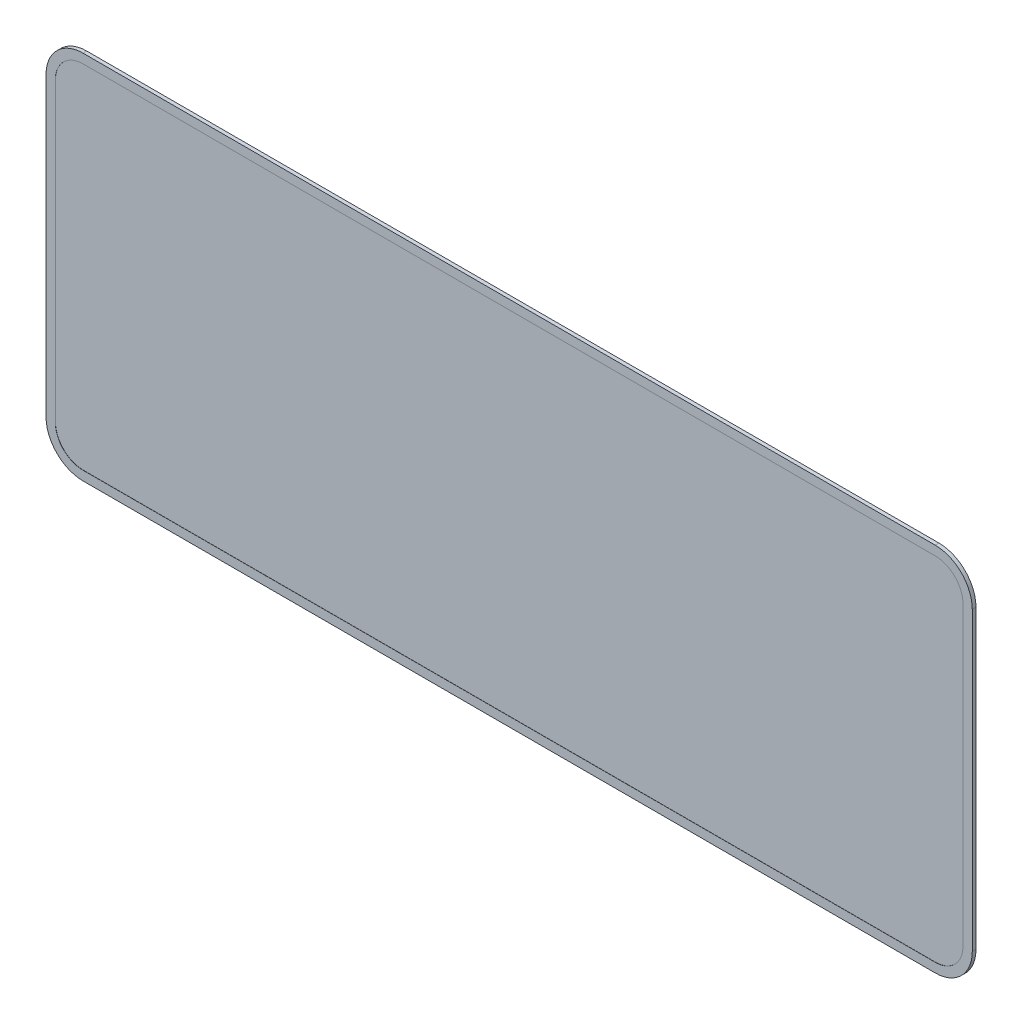
SolidWorks part; units mm, degrees
ref_plane "Ön Düzlem" through (0, 0, 0) normal (0, 0, 1) x (1, 0, 0)
ref_plane "Üst Düzlem" through (0, 0, 0) normal (0, 1, 0) x (1, 0, 0)
ref_plane "Sağ Düzlem" through (0, 0, 0) normal (1, 0, 0) x (0, 0, -1)
sketch "Sketch1" plane through (0, 0, 0) normal (0, 0, 1) x (1, 0, 0)
  line L1 (20, 0) -> (480, 0)
  line L2 (0, 20) -> (0, 180)
  line L3 (20, 200) -> (480, 200)
  line L4 (500, 20) -> (500, 180)
  arc A0 (480, 0) -> (500, 20) centre (480, 20) ccw
  arc A1 (20, 0) -> (0, 20) centre (20, 20) cw
  arc A2 (0, 180) -> (20, 200) centre (20, 180) cw
  arc A3 (480, 200) -> (500, 180) centre (480, 180) cw
  point P9 (0, 0)
  point P12 (0, 200)
  point P15 (500, 200)
  dimension "D3" = 20
  dimension "D1" = 500
  dimension "D2" = 200
extrude "Boss-Extrude1" add sketch "Sketch1" along normal blind 2
sketch "Sketch3" plane through (0, 0, 2) normal (0, 0, 1) x (1, 0, 0)
  line L8 (495, 20) -> (495, 180)
  line L9 (480, 195) -> (20, 195)
  line L10 (5, 180) -> (5, 20)
  line L11 (20, 5) -> (480, 5)
  line L12 (495, 20) -> (495, 180)
  line L13 (480, 195) -> (20, 195)
  line L14 (5, 180) -> (5, 20)
  line L15 (20, 5) -> (480, 5)
  arc A8 (480, 5) -> (495, 20) centre (480, 20) ccw
  arc A9 (495, 180) -> (480, 195) centre (480, 180) ccw
  arc A10 (20, 195) -> (5, 180) centre (20, 180) ccw
  arc A11 (5, 20) -> (20, 5) centre (20, 20) ccw
  arc A12 (480, 5) -> (495, 20) centre (480, 20) ccw
  arc A13 (495, 180) -> (480, 195) centre (480, 180) ccw
  arc A14 (20, 195) -> (5, 180) centre (20, 180) ccw
  arc A15 (5, 20) -> (20, 5) centre (20, 20) ccw
  dimension "D1" = 5
extrude "Cut-Extrude1" cut sketch "Sketch3" against normal blind 0.1
